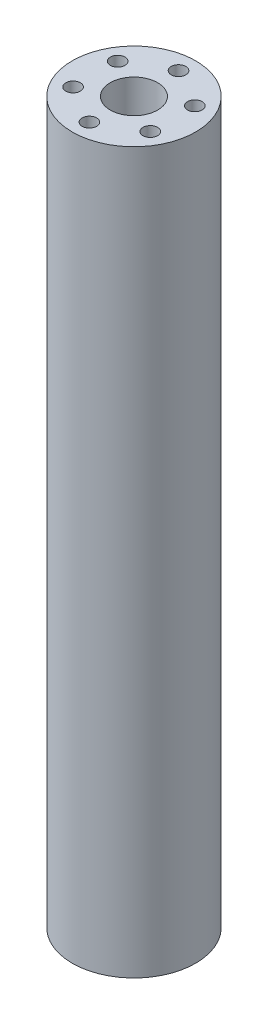
SolidWorks part; units mm, degrees
material "Natural Rubber"
ref_plane "Front Plane" through (0, 0, 0) normal (0, 0, 1) x (1, 0, 0)
ref_plane "Top Plane" through (0, 0, 0) normal (0, 1, 0) x (1, 0, 0)
ref_plane "Right Plane" through (0, 0, 0) normal (1, 0, 0) x (0, 0, -1)
sketch "Sketch1" plane through (0, 0, 0) normal (0, 1, 0) x (1, 0, 0)
  circle A0 centre (0, 0) radius 18
  circle A1 centre (0, 13) radius 2.1277
  circle A2 centre (0, 0) radius 6.9156
  circle A3 centre (11.2583, 6.5) radius 2.1277
  circle A4 centre (11.2583, -6.5) radius 2.1277
  circle A5 centre (0, -13) radius 2.1277
  circle A6 centre (-11.2583, -6.5) radius 2.1277
  circle A7 centre (-11.2583, 6.5) radius 2.1277
  point P18 (0, 0)
  dimension "D1" = 13.8313
  dimension "D3" = 4.2554
  dimension "D6" = 36
  dimension "D4" = 13
  dimension "D5" = 6
extrude "Boss-Extrude1" add sketch "Sketch1" along normal blind 210
